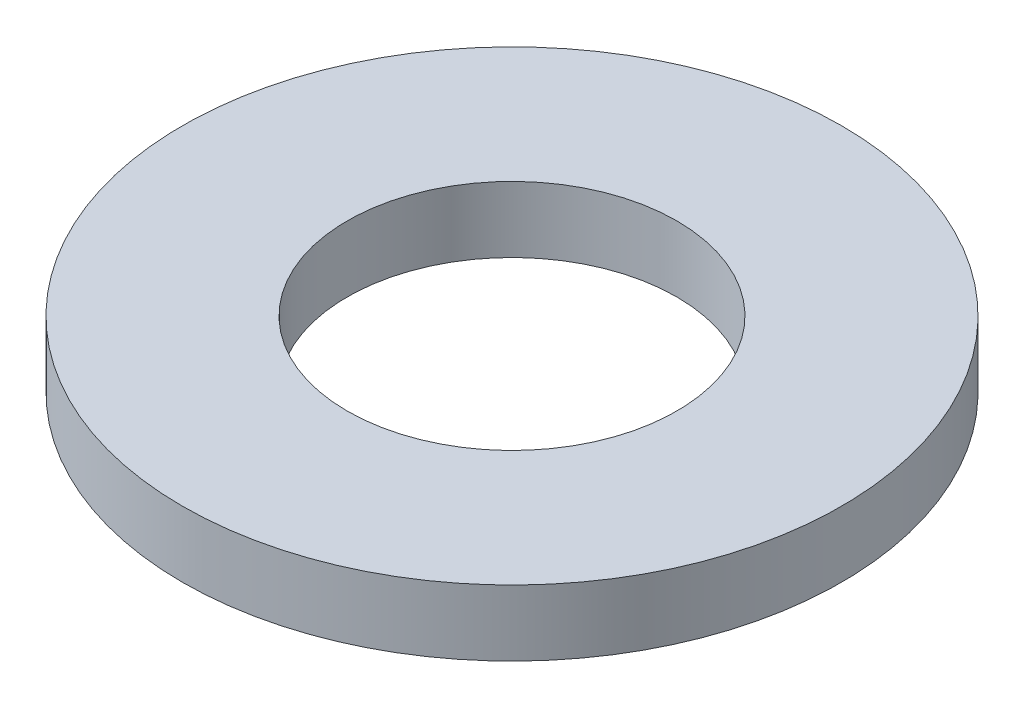
SolidWorks part; units mm, degrees
ref_plane "Plan de face" through (0, 0, 0) normal (0, 0, 1) x (1, 0, 0)
ref_plane "Plan de dessus" through (0, 0, 0) normal (0, 1, 0) x (1, 0, 0)
ref_plane "Plan de droite" through (0, 0, 0) normal (1, 0, 0) x (0, 0, -1)
sketch "Esquisse1" plane through (0, 0, 0) normal (0, 1, 0) x (1, 0, 0)
  circle A0 centre (0, 0) radius 5
  circle A1 centre (0, 0) radius 2.5
  dimension "D1" = 10
  dimension "D2" = 5
extrude "Boss.-Extru.1" add sketch "Esquisse1" along normal blind 1
